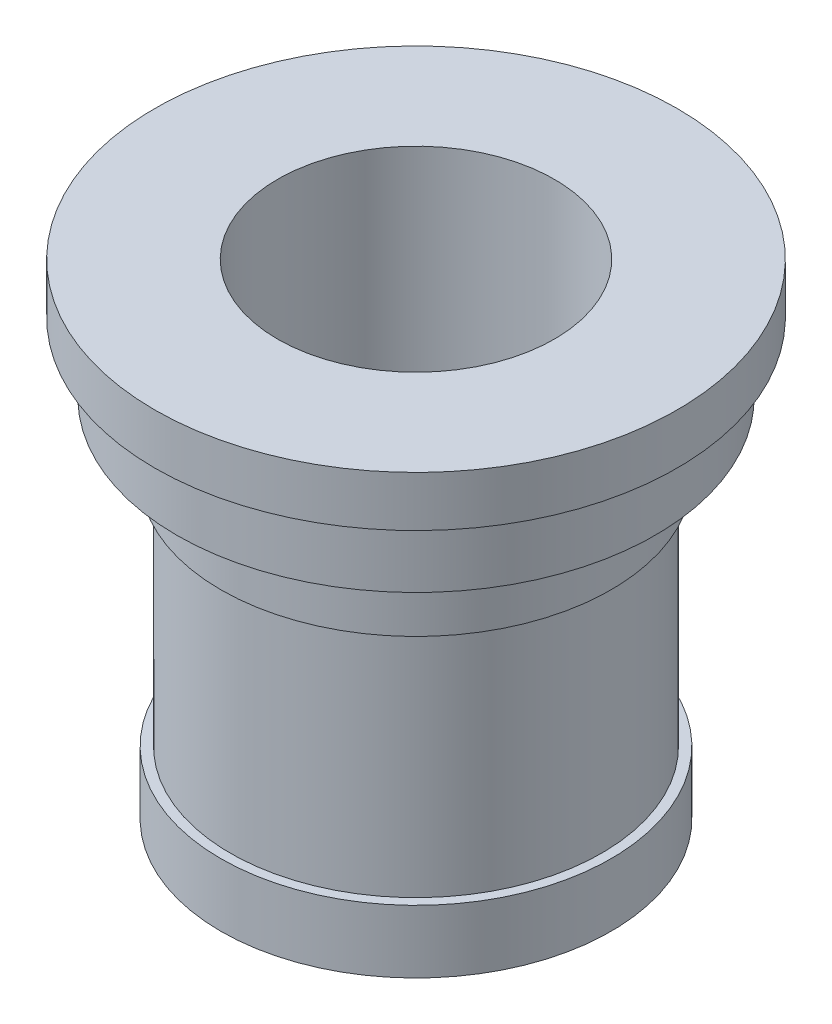
SolidWorks part; units mm, degrees
ref_plane "Front Plane" through (0, 0, 0) normal (0, 0, 1) x (1, 0, 0)
ref_plane "Top Plane" through (0, 0, 0) normal (0, 1, 0) x (1, 0, 0)
ref_plane "Right Plane" through (0, 0, 0) normal (1, 0, 0) x (0, 0, -1)
sketch "Sketch1" plane through (0, 0, 0) normal (0, 0, 1) x (1, 0, 0)
  line L0 (0, 0) -> (0, 100.8696) construction
  line L1 (0, 0) -> (31, 0)
  line L2 (31, 0) -> (31, 10)
  line L3 (31, 10) -> (29.5, 10)
  line L4 (29.5, 10) -> (29.5, 47)
  line L5 (29.5, 47) -> (31, 47)
  line L6 (31, 47) -> (31, 58)
  line L7 (31, 58) -> (38, 58)
  line L8 (38, 58) -> (38, 69)
  line L9 (38, 69) -> (41.5, 69)
  line L10 (41.5, 69) -> (41.5, 77)
  line L11 (41.5, 77) -> (0, 77)
  line L12 (0, 77) -> (0, 0)
  dimension "D1" = 10
  dimension "D2" = 37
  dimension "D3" = 11
  dimension "D4" = 11
  dimension "D5" = 8
  dimension "D6" = 11
  dimension "D7" = 83
  dimension "D8" = 76
  dimension "D9" = 62
  dimension "D10" = 59
  dimension "D11" = 62
revolve "Revolve1" add sketch "Sketch1" angle 360 about L0
sketch "Sketch2" plane through (0, 77, 0) normal (0, 1, 0) x (1, 0, 0)
  circle A0 centre (0, 0) radius 22
  dimension "D1" = 44
extrude "Cut-Extrude1" cut sketch "Sketch2" against normal blind 77
